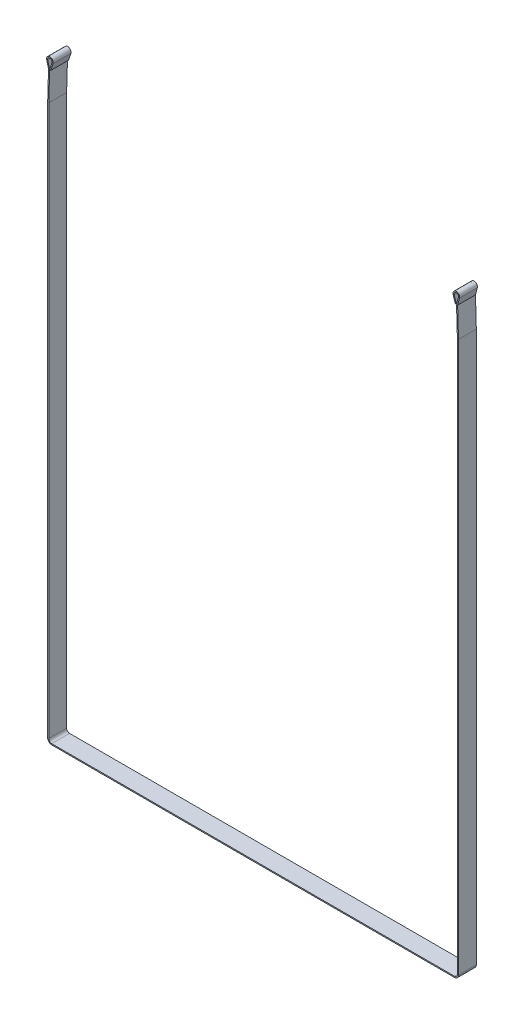
SolidWorks part; units mm, degrees
material "PP copolymère"
ref_plane "Plan1" through (0, 0, 0) normal (0, 0, 1) x (1, 0, 0)
ref_plane "Plan2" through (0, 0, 0) normal (0, 1, 0) x (1, 0, 0)
ref_plane "Plan3" through (0, 0, 0) normal (1, 0, 0) x (0, 0, -1)
sketch "Esquisse1" plane through (0, 0, 0) normal (0, 0, 1) x (1, 0, 0)
  line L0 (542, -1570) -> (-542, -1570)
  line L1 (-550, -80) -> (-547.6657, -0.87)
  line L2 (0, 0) -> (0, -1570) construction
  line L3 (550, -1562) -> (550, -80)
  line L4 (-547, 26) -> (547, 26) construction
  line L5 (-550, -1562) -> (-550, -80)
  line L6 (-541.3019, 18.1208) -> (-547.5657, -0.8729)
  line L7 (541.3019, 18.1208) -> (547.5657, -0.8729)
  line L8 (550, -80) -> (547.6657, -0.87)
  line L10 (-547.5657, -0.8729) -> (-547.6657, -0.87) construction
  line L11 (-547.6157, -0.8715) -> (-547, 20) construction
  line L12 (-552.799, 18.46) -> (-547.6657, -0.87)
  line L13 (552.799, 18.46) -> (547.6657, -0.87)
  arc A0 (550, -1562) -> (542, -1570) centre (542, -1562) cw
  arc A1 (-552.799, 18.46) -> (-547, 26) centre (-547, 20) cw
  arc A2 (552.799, 18.46) -> (547, 26) centre (547, 20) ccw
  arc A3 (-550, -1562) -> (-542, -1570) centre (-542, -1562) ccw
  arc A4 (-541.3019, 18.1208) -> (-547, 26) centre (-547, 20) ccw
  arc A5 (541.3019, 18.1208) -> (547, 26) centre (547, 20) cw
  dimension "D2" = 8
  dimension "D5" = 1100
  dimension "D9" = 6
  dimension "D3" = 20
  dimension "D4" = 1490
  dimension "D6" = 3
  dimension "D7" = 20
  dimension "D8" = 80
  dimension "D10" = 0.1
extrude "Extru.-Mince1" add sketch "Esquisse1" along normal mid plane 48 thin thin type one direction wall 3
